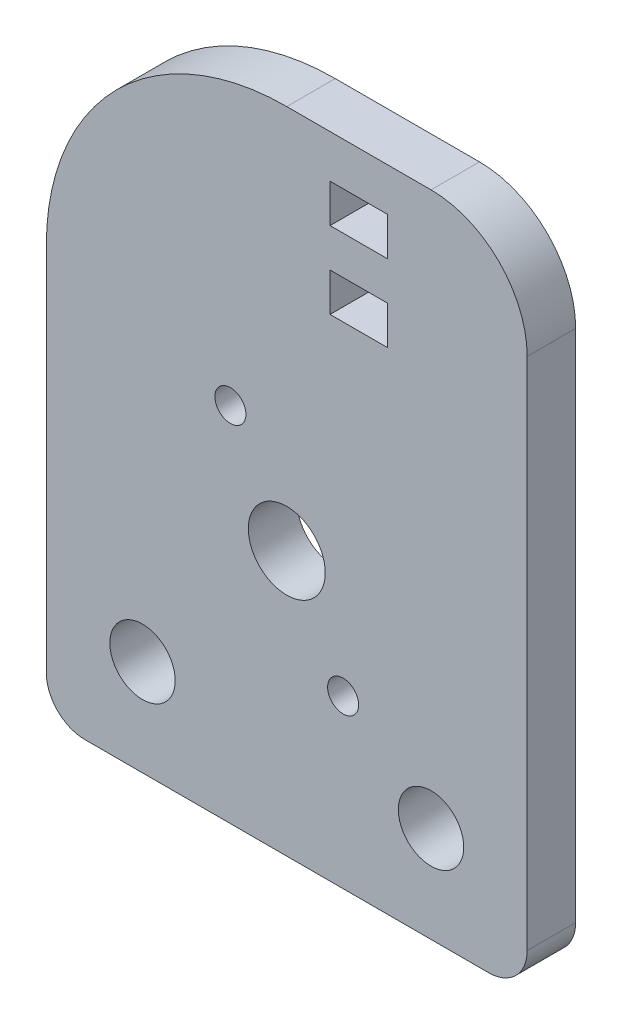
SolidWorks part; units mm, degrees
ref_plane "Front Plane" through (0, 0, 0) normal (0, 0, 1) x (1, 0, 0)
ref_plane "Top Plane" through (0, 0, 0) normal (0, 1, 0) x (1, 0, 0)
ref_plane "Right Plane" through (0, 0, 0) normal (1, 0, 0) x (0, 0, -1)
sketch "Sketch1" plane through (0, 0, 0) normal (0, 0, 1) x (1, 0, 0)
  line L0 (0, 0) -> (0, -11.1125) construction
  line L1 (-9.525, -11.1125) -> (9.525, -11.1125) construction
  line L2 (15.875, 25.4) -> (15.875, 9.525)
  line L4 (-15.875, 9.525) -> (-15.875, -17.4625)
  line L5 (-15.875, -17.4625) -> (15.875, -17.4625)
  line L6 (15.875, 9.525) -> (15.875, -17.4625)
  line L7 (0, 25.4) -> (15.875, 25.4)
  line L8 (-15.875, 0) -> (15.875, 0) construction
  circle A1 centre (0, 0) radius 2.54
  circle A2 centre (-9.525, -11.1125) radius 2.159
  circle A3 centre (9.525, -11.1125) radius 2.159
  arc A6 (0, 25.4) -> (-15.875, 9.525) centre (0, 9.525) ccw
  dimension "D1" = 5.08
  dimension "D2" = 31.75
  dimension "D4" = 4.318
  dimension "D7" = 15.875
  dimension "D3" = 19.05
  dimension "D5" = 11.1125
  dimension "D6" = 6.35
  dimension "D8" = 9.525
extrude "Boss-Extrude1" add sketch "Sketch1" along normal blind 3.2004
fillet "Fillet1" radius 6.35 1 edges at (15.875, 25.4, 1.6002)
fillet "Fillet2" radius 2.54 2 edges at (-15.875, -17.4625, 1.6002) (15.875, -17.4625, 1.6002)
sketch "Sketch2" plane through (0, 0, 3.2004) normal (0, 0, 1) x (1, 0, 0)
  circle A0 centre (-3.7211, 6.4451) radius 1.025
  circle A1 centre (3.7211, -6.4451) radius 1.025
  circle A2 centre (-3.7211, 6.4451) radius 1.397 construction
  circle A3 centre (3.7211, -6.4451) radius 1.397 construction
  dimension "D1" = 2.05
extrude "Cut-Extrude1" cut sketch "Sketch2" against normal up to surface (3.2004 mm away) up to face at (0.944, 2.2695, 0)
sketch "Sketch3" plane through (0, 0, 3.2004) normal (0, 0, 1) x (1, 0, 0)
  line L0 (4.7625, 21.2928) -> (4.7625, 16.2128) construction
  line L5 (15.875, -14.9225) -> (15.875, 19.05) construction
  line L8 (4.7625, 25.4) -> (4.7625, 21.2928) construction
  line L9 (9.525, 25.4) -> (0, 25.4) construction
  line L11 (2.8575, 21.2928) -> (6.6675, 21.2928) construction
  line L12 (2.8575, 22.5628) -> (6.6675, 22.5628)
  line L13 (2.8575, 22.5628) -> (2.8575, 20.0228)
  line L14 (2.8575, 20.0228) -> (6.6675, 20.0228)
  line L15 (6.6675, 22.5628) -> (6.6675, 20.0228)
  line L20 (2.8575, 16.2128) -> (6.6675, 16.2128) construction
  line L21 (2.8575, 17.4828) -> (6.6675, 17.4828)
  line L22 (2.8575, 17.4828) -> (2.8575, 14.9428)
  line L23 (2.8575, 14.9428) -> (6.6675, 14.9428)
  line L24 (6.6675, 17.4828) -> (6.6675, 14.9428)
  dimension "D5" = 2.54
  dimension "D6" = 3.81
  dimension "D7" = 5.08
extrude "Cut-Extrude2" cut sketch "Sketch3" against normal up to surface (3.2004 mm away) up to face at (-2.6961, 6.4451, 0)
